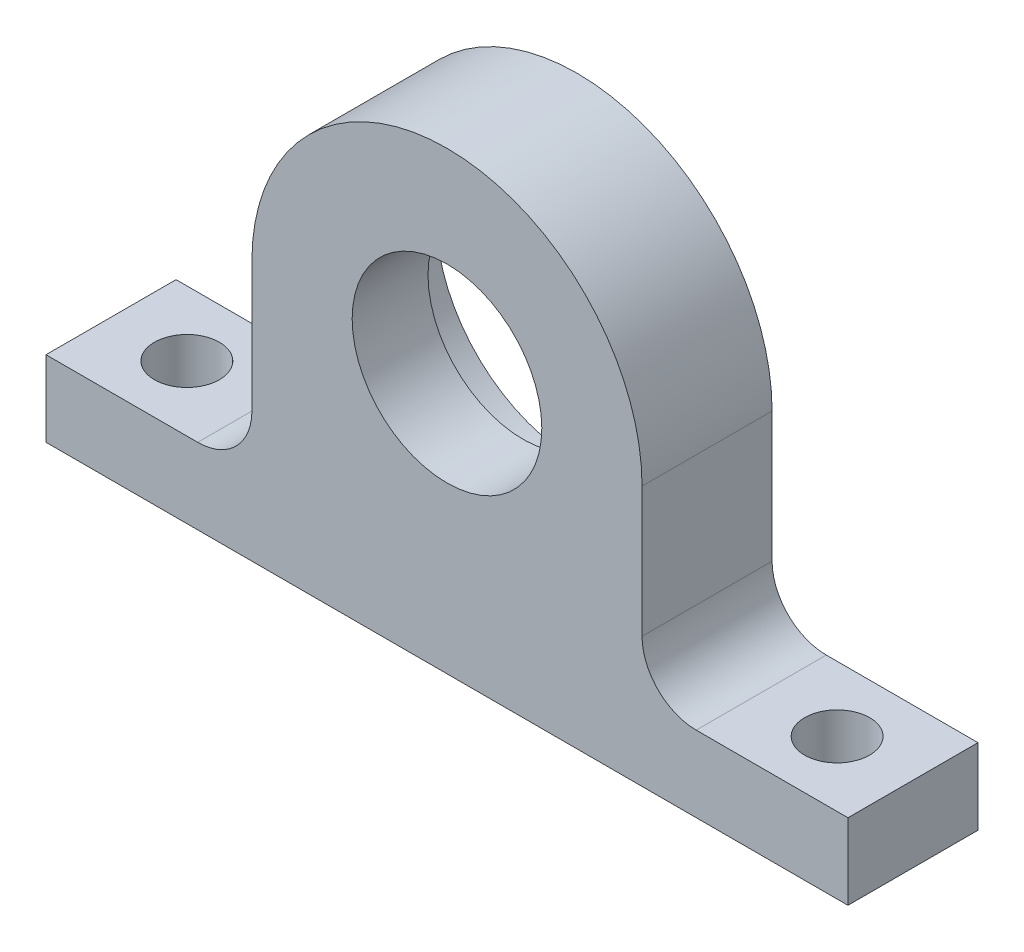
SolidWorks part; units mm, degrees
material "6061-T6 (SS)"
ref_plane "Front Plane" through (0, 0, 0) normal (0, 0, 1) x (1, 0, 0)
ref_plane "Top Plane" through (0, 0, 0) normal (0, 1, 0) x (1, 0, 0)
ref_plane "Right Plane" through (0, 0, 0) normal (1, 0, 0) x (0, 0, -1)
sketch "Sketch1" plane through (0, 0, 0) normal (0, 0, 1) x (1, 0, 0)
  line L0 (-5.9161, -17) -> (-37, -17)
  line L1 (-37, -17) -> (-37, -24)
  line L2 (-37, -24) -> (0, -24)
  line L3 (0, 0) -> (0, 38.453) construction
  line L4 (37, -24) -> (0, -24)
  line L5 (37, -17) -> (37, -24)
  line L6 (5.9161, -17) -> (37, -17)
  circle A0 centre (0, 0) radius 8.75
  arc A2 (5.9161, -17) -> (-5.9161, -17) centre (0, 0) ccw
  point P16 (-5.9161, -17)
  point P19 (5.9161, -17)
  dimension "D2" = 74
  dimension "D3" = 17
  dimension "D5" = 18
  dimension "D4" = 7
extrude "Boss-Extrude1" add sketch "Sketch1" along normal blind 12
sketch "Sketch2" plane through (0, -17, 0) normal (0, 1, 0) x (1, 0, 0)
  line L0 (37, -12) -> (37, 0) construction
  line L2 (0, 0) -> (0, 23.6093) construction
  circle A0 centre (30, -6) radius 3
  circle A1 centre (-30, -6) radius 3
  point P5 (37, -6)
  dimension "D1" = 6
  dimension "D2" = 7
extrude "Cut-Extrude1" cut sketch "Sketch2" against normal through all
sketch "Sketch3" plane through (0, 0, 0) normal (0, 0, -1) x (-1, 0, 0)
  circle A0 centre (0, 0) radius 13
  dimension "D1" = 26
extrude "Cut-Extrude2" cut sketch "Sketch3" against normal blind 5
sketch "Sketch4" plane through (0, 0, 0) normal (0, 0, -1) x (-1, 0, 0)
  line L1 (-18, 0) -> (-5.9161, -17)
  line L2 (-5.9161, -17) -> (-18, -17)
  line L3 (0, 0) -> (0, -6.2592) construction
  line L4 (18, 0) -> (18, -17)
  line L5 (5.9161, -17) -> (18, -17)
  line L6 (-18, 0) -> (-18, -17)
  line L7 (18, 0) -> (5.9161, -17)
  arc A1 (5.9161, -17) -> (-5.9161, -17) centre (0, 0) ccw construction
extrude "Boss-Extrude2" add sketch "Sketch4" against normal through all
fillet "Fillet2" radius 5 2 edges at (-18, -17, 6) (18, -17, 6)
